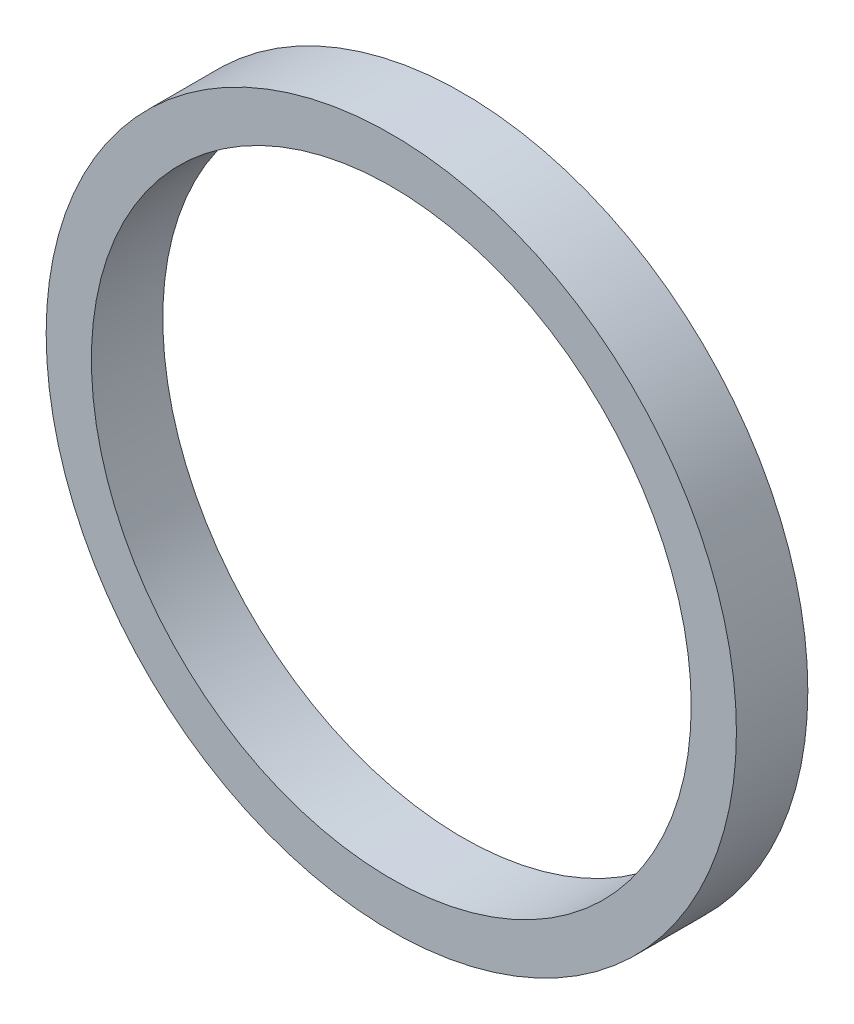
SolidWorks part; units mm, degrees
material "Alumine"
ref_plane "Plan de face" through (0, 0, 0) normal (0, 0, 1) x (1, 0, 0)
ref_plane "Plan de dessus" through (0, 0, 0) normal (0, 1, 0) x (1, 0, 0)
ref_plane "Plan de droite" through (0, 0, 0) normal (1, 0, 0) x (0, 0, -1)
sketch "Esquisse1" plane through (0, 0, 0) normal (0, 0, 1) x (1, 0, 0)
  circle A0 centre (0, 0) radius 14.5
  circle A1 centre (0, 0) radius 12.6
  dimension "D1" = 25.2
  dimension "D2" = 29
extrude "Boss.-Extru.1" add sketch "Esquisse1" along normal blind 3
